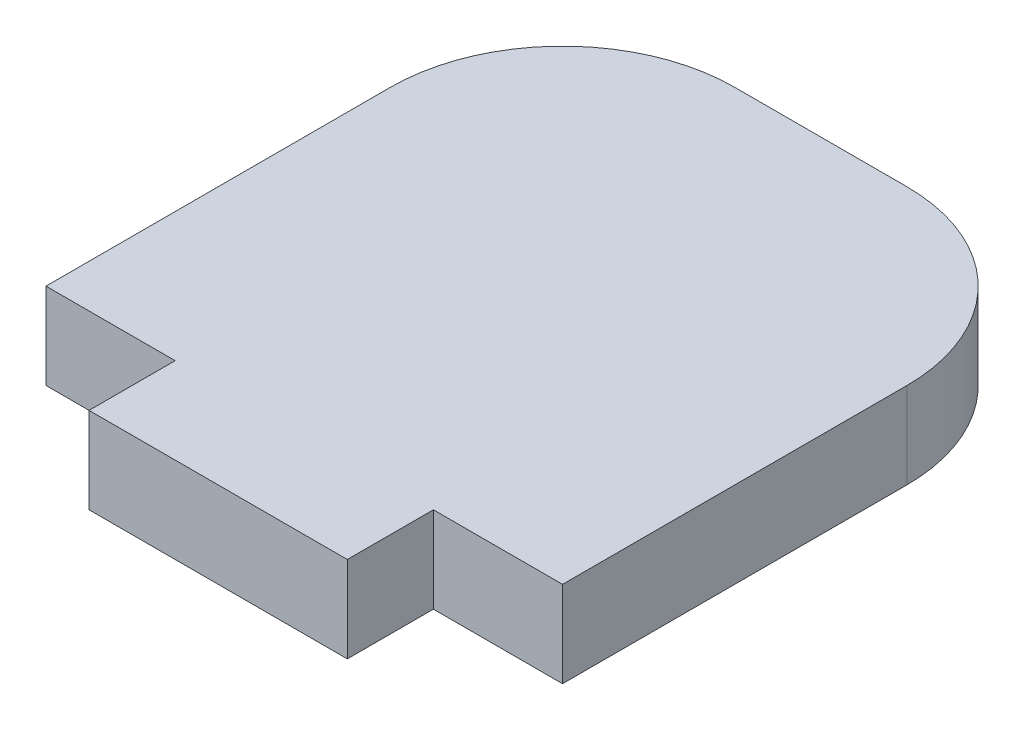
SolidWorks part; units mm, degrees
ref_plane "Front Plane" through (0, 0, 0) normal (0, 0, 1) x (1, 0, 0)
ref_plane "Top Plane" through (0, 0, 0) normal (0, 1, 0) x (1, 0, 0)
ref_plane "Right Plane" through (0, 0, 0) normal (1, 0, 0) x (0, 0, -1)
sketch "Sketch1" plane through (0, 0, 0) normal (0, 1, 0) x (1, 0, 0)
  line L0 (0, 41.275) -> (0, 3.175) construction
  line L1 (9.525, -3.175) -> (-9.525, -3.175)
  line L2 (9.525, -3.175) -> (9.525, 3.175)
  line L4 (-9.525, -3.175) -> (-9.525, 3.175)
  line L5 (9.525, -3.175) -> (-9.525, 3.175) construction
  line L6 (9.525, 3.175) -> (-9.525, -3.175) construction
  line L7 (-19.05, 3.175) -> (-9.525, 3.175)
  line L8 (-19.05, 3.175) -> (-19.05, 28.575)
  line L9 (-6.35, 41.275) -> (6.35, 41.275)
  line L10 (19.05, 3.175) -> (19.05, 28.575)
  line L11 (9.525, 3.175) -> (19.05, 3.175)
  arc A0 (6.35, 41.275) -> (19.05, 28.575) centre (6.35, 28.575) cw
  arc A1 (-19.05, 28.575) -> (-6.35, 41.275) centre (-6.35, 28.575) cw
  point P0 (0, 0)
  point P14 (19.05, 41.275)
  point P17 (-19.05, 41.275)
  dimension "D6" = 12.7
  dimension "D1" = 6.35
  dimension "D2" = 19.05
  dimension "D3" = 0
  dimension "D4" = 38.1
  dimension "D5" = 38.1
extrude "Boss-Extrude1" add sketch "Sketch1" along normal blind 6.35
